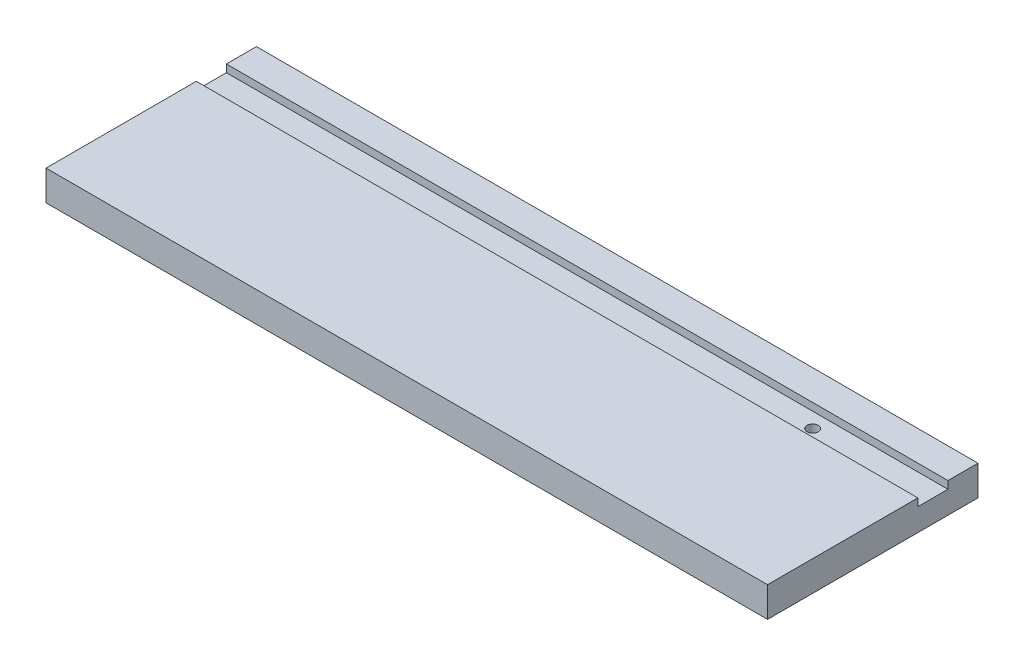
SolidWorks part; units mm, degrees
ref_plane "Front Plane" through (0, 0, 0) normal (0, 0, 1) x (1, 0, 0)
ref_plane "Top Plane" through (0, 0, 0) normal (0, 1, 0) x (1, 0, 0)
ref_plane "Right Plane" through (0, 0, 0) normal (1, 0, 0) x (0, 0, -1)
sketch "Sketch1" plane through (0, 0, 0) normal (0, 1, 0) x (1, 0, 0)
  line L1 (0, 0) -> (152.4, 0)
  line L2 (0, 0) -> (0, 44.45)
  line L3 (0, 44.45) -> (152.4, 44.45)
  line L4 (152.4, 0) -> (152.4, 44.45)
  dimension "D1" = 44.45
  dimension "D2" = 152.4
extrude "Boss-Extrude2" add sketch "Sketch1" along normal blind 6.35
sketch "Sketch2" plane through (0, 6.35, 0) normal (0, 1, 0) x (1, 0, 0)
  line L0 (152.4, 0) -> (152.4, 44.45) construction
  line L1 (152.4, 38.1) -> (6.35, 38.1)
  line L2 (152.4, 38.1) -> (152.4, 31.75)
  line L3 (152.4, 31.75) -> (6.35, 31.75)
  line L4 (6.35, 38.1) -> (6.35, 31.75)
  line L5 (152.4, 44.45) -> (0, 44.45) construction
  line L6 (0, 44.45) -> (0, 0) construction
  dimension "D1" = 6.35
  dimension "D2" = 6.35
  dimension "D3" = 6.35
extrude "Cut-Extrude1" cut sketch "Sketch2" against normal blind 1.6002
sketch "Sketch3" plane through (0, 4.7498, 0) normal (0, 1, 0) x (1, 0, 0)
  line L0 (6.35, 34.925) -> (152.4, 34.925) construction
  line L1 (6.35, 38.1) -> (6.35, 31.75) construction
  line L2 (152.4, 31.75) -> (152.4, 38.1) construction
  circle A0 centre (127, 34.925) radius 1.1875
  dimension "D1" = 25.4
extrude "Cut-Extrude2" cut sketch "Sketch3" against normal through all
sketch "Sketch4" plane through (0, 6.35, 0) normal (0, 1, 0) x (1, 0, 0)
  line L0 (0, 44.45) -> (0, 0) construction
  line L1 (6.35, 38.1) -> (0, 38.1)
  line L2 (6.35, 38.1) -> (6.35, 31.75)
  line L3 (6.35, 31.75) -> (0, 31.75)
  line L4 (0, 38.1) -> (0, 31.75)
extrude "Cut-Extrude4" cut sketch "Sketch4" against normal blind 1.6002
